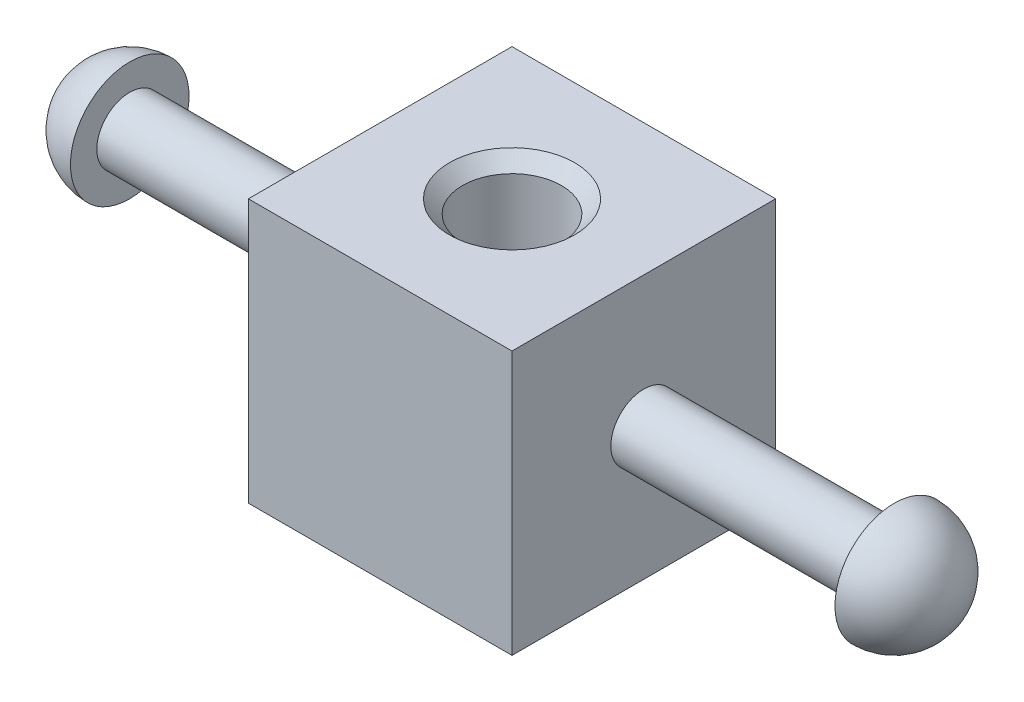
SolidWorks part; units mm, degrees
material "AISI 1020"
ref_plane "Front Plane" through (0, 0, 0) normal (0, 0, 1) x (1, 0, 0)
ref_plane "Top Plane" through (0, 0, 0) normal (0, 1, 0) x (1, 0, 0)
ref_plane "Right Plane" through (0, 0, 0) normal (1, 0, 0) x (0, 0, -1)
sketch "Sketch1" plane through (0, 0, 0) normal (0, 1, 0) x (1, 0, 0)
  line L1 (-12.7, -12.7) -> (12.7, -12.7)
  line L2 (-12.7, -12.7) -> (-12.7, 12.7)
  line L3 (-12.7, 12.7) -> (12.7, 12.7)
  line L4 (12.7, -12.7) -> (12.7, 12.7)
  line L5 (-12.7, -12.7) -> (12.7, 12.7) construction
  line L6 (-12.7, 12.7) -> (12.7, -12.7) construction
  circle A0 centre (0, 0) radius 4.7625
  point P0 (0, 0)
  dimension "D2" = 9.525
  dimension "D1" = 25.4
extrude "Boss-Extrude1" add sketch "Sketch1" along normal blind 25.4
chamfer "Chamfer1" distance 1.27 angle 45 2 edges at (0, 0, 4.7625) (0, 25.4, 4.7625)
ref_plane "Plane1" through (0, 12.7, 0) normal (0, 1, 0) x (1, 0, 0)
sketch "Sketch2" plane through (0, 12.7, 0) normal (0, 1, 0) x (1, 0, 0)
  line L1 (-36.83, -3.175) -> (36.83, -3.175)
  line L8 (36.83, -3.175) -> (36.83, -5.715)
  line L9 (-42.545, 0) -> (42.545, 0)
  line L10 (-36.83, -3.175) -> (-36.83, -5.715)
  arc A1 (-42.545, 0) -> (-36.83, -5.715) centre (-36.83, 0) ccw
  arc A2 (42.545, 0) -> (36.83, -5.715) centre (36.83, 0) cw
  point P0 (0, 0)
revolve "Revolve1" add sketch "Sketch2" angle 360 about L9
sketch "Sketch3" plane through (0, 25.4, 0) normal (0, 1, 0) x (1, 0, 0)
  circle A0 centre (0, 0) radius 4.7625
extrude "Cut-Extrude1" cut sketch "Sketch3" against normal through all
